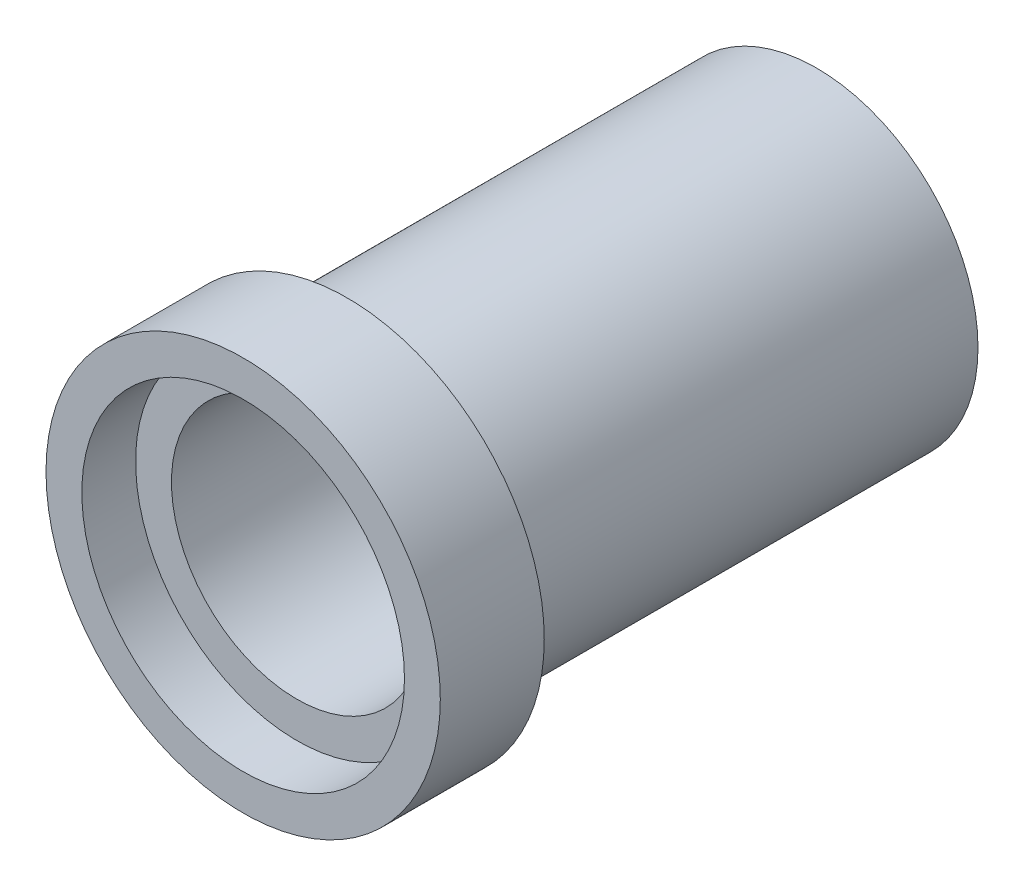
SolidWorks part; units mm, degrees
ref_plane "Front Plane" through (0, 0, 0) normal (0, 0, 1) x (1, 0, 0)
ref_plane "Top Plane" through (0, 0, 0) normal (0, 1, 0) x (1, 0, 0)
ref_plane "Right Plane" through (0, 0, 0) normal (1, 0, 0) x (0, 0, -1)
sketch "Sketch2" plane through (0, 0, 0) normal (1, 0, 0) x (0, 0, -1)
  line L0 (-152.2376, 0) -> (156.2368, 0) construction
  line L1 (0, 65.2405) -> (0, -69.9124) construction
  line L2 (-16, 11) -> (-10.2, 11)
  line L3 (-10.2, 11) -> (-10.2, 9)
  line L4 (-10.2, 9) -> (16, 9)
  line L5 (-16, 9) -> (-12.2, 9)
  line L6 (-12.2, 9) -> (-12.2, 7)
  line L7 (-12.2, 7) -> (16, 7)
  line L8 (-16, 9) -> (-16, 11)
  line L9 (16, 7) -> (16, 9)
  dimension "D1" = 18
  dimension "D2" = 5.8
  dimension "D3" = 22
  dimension "D5" = 32
  dimension "D4" = 2
revolve "Revolve1" add sketch "Sketch2" angle 360 about L0
sketch "Sketch3" plane through (0, 0, 12.2) normal (0, 0, 1) x (1, 0, 0)
  circle A0 centre (0, 0) radius 7 construction
  circle A1 centre (0, 0) radius 9
  circle A2 centre (0, 0) radius 9
  circle A3 centre (0, 0) radius 7
  dimension "D1" = 0
extrude "Boss-Extrude1" add sketch "Sketch3" along normal blind 0.8
